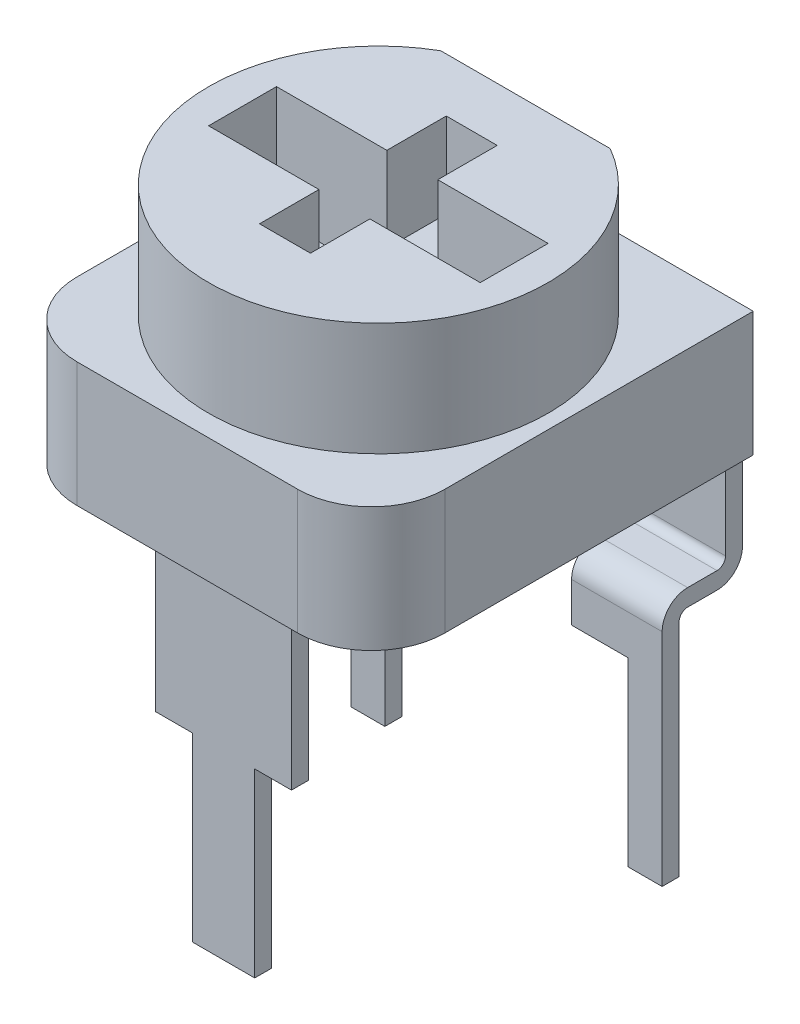
SolidWorks part; units mm, degrees
ref_plane "Plan de face" through (0, 0, 0) normal (0, 0, 1) x (1, 0, 0)
ref_plane "Plan de dessus" through (0, 0, 0) normal (0, 1, 0) x (1, 0, 0)
ref_plane "Plan de droite" through (0, 0, 0) normal (1, 0, 0) x (0, 0, -1)
sketch "Esquisse1" plane through (0, 0, 0) normal (0, 1, 0) x (1, 0, 0)
  line L0 (-1.4967, 2.6) -> (1.4967, 2.6)
  line L2 (-2.4, -0.6) -> (2.4, -0.6)
  line L3 (-2.4, -0.6) -> (-2.4, 0.6)
  line L4 (-2.4, 0.6) -> (2.4, 0.6)
  line L5 (2.4, -0.6) -> (2.4, 0.6)
  line L6 (-2.4, -0.6) -> (2.4, 0.6) construction
  line L7 (-2.4, 0.6) -> (2.4, -0.6) construction
  arc A0 (-1.4967, 2.6) -> (1.4967, 2.6) centre (0, 0) ccw
  dimension "D1" = 3
  dimension "D2" = 2.6
  dimension "D3" = 4.8
  dimension "D4" = 1.2
extrude "Boss.-Extru.1" add sketch "Esquisse1" along normal blind 2
sketch "Esquisse2" plane through (0, 2, 0) normal (0, 1, 0) x (-1, 0, 0)
  line L1 (0.45, 1.65) -> (-0.45, 1.65)
  line L2 (0.45, 1.65) -> (0.45, -1.65)
  line L3 (0.45, -1.65) -> (-0.45, -1.65)
  line L4 (-0.45, 1.65) -> (-0.45, -1.65)
  line L5 (0.45, 1.65) -> (-0.45, -1.65) construction
  line L6 (0.45, -1.65) -> (-0.45, 1.65) construction
  point P0 (0, 0)
  dimension "D1" = 0.9
  dimension "D2" = 3.3
extrude "Enlèv. mat.-Extru.1" cut sketch "Esquisse2" against normal blind 1.5
sketch "Esquisse3" plane through (0, 0, 0) normal (0, 1, 0) x (1, 0, 0)
  line L1 (-1.95, -3.375) -> (1.95, -3.375)
  line L2 (-3.25, -2.075) -> (-3.25, 3.375)
  line L3 (-3.25, 3.375) -> (3.25, 3.375)
  line L4 (3.25, -2.075) -> (3.25, 3.375)
  line L5 (-3.25, -3.375) -> (3.25, 3.375) construction
  line L6 (-3.25, 3.375) -> (3.25, -3.375) construction
  arc A0 (1.95, -3.375) -> (3.25, -2.075) centre (1.95, -2.075) ccw
  arc A1 (-1.95, -3.375) -> (-3.25, -2.075) centre (-1.95, -2.075) cw
  point P0 (0, 0)
  dimension "D3" = 1.3
  dimension "D1" = 6.5
  dimension "D2" = 6.75
  dimension "D4" = 3.375
extrude "Boss.-Extru.2" add sketch "Esquisse3" against normal blind 2.2
sketch "Esquisse4" plane through (0, 0, 0) normal (1, 0, 0) x (0, 0, -1)
  line L0 (0.5438, -1) -> (3.235, -1)
  line L1 (3.535, -1.3) -> (3.535, -4)
  line L2 (3.235, -4.3) -> (2.715, -4.3)
  line L3 (2.415, -4.6) -> (2.415, -8.5)
  line L4 (3.375, -2.2) -> (3.375, 0) construction
  line L5 (-2.075, 0) -> (3.375, 0) construction
  arc A0 (2.715, -4.3) -> (2.415, -4.6) centre (2.715, -4.6) ccw
  arc A1 (3.535, -4) -> (3.235, -4.3) centre (3.235, -4) cw
  arc A2 (3.235, -1) -> (3.535, -1.3) centre (3.235, -1.3) cw
  dimension "D1" = 0.3
  dimension "D2" = 1.12
  dimension "D3" = 7.5
  dimension "D4" = 4.2
  dimension "D5" = 0.16
  dimension "D6" = 1
extrude "Extru.-Mince1" add sketch "Esquisse4" along normal mid plane 1.6 from offset 1.95 thin offset against normal yes
pattern_linear "Répétition linéaire1" count 2 spacing 3.9 along (1, 0, 0) of "Extru.-Mince1"
sketch "Esquisse5" plane through (0, 0, 0) normal (1, 0, 0) x (0, 0, -1)
  line L0 (-2.585, -8.5) -> (-2.585, -2.2)
  line L1 (-2.075, -2.2) -> (3.375, -2.2) construction
  line L2 (2.565, -8.5) -> (2.265, -8.5) construction
  point P5 (2.415, -8.5)
  dimension "D1" = 5
extrude "Extru.-Mince2" add sketch "Esquisse5" along normal mid plane 2.4 thin thin type mid plane wall 0.3
sketch "Esquisse6" plane through (0, 0, -2.565) normal (0, 0, -1) x (-1, 0, 0)
  line L0 (-2.75, -8.5) -> (-1.15, -8.5) construction
  line L1 (-2.15, -8.5) -> (-0.55, -8.5)
  line L2 (-2.15, -8.5) -> (-2.15, -5.3)
  line L3 (-2.15, -5.3) -> (-0.55, -5.3)
  line L4 (-0.55, -8.5) -> (-0.55, -5.3)
  line L5 (-2.75, -4.6) -> (-2.75, -8.5) construction
  line L6 (1.15, -8.5) -> (2.75, -8.5) construction
  line L7 (0.55, -5.3) -> (2.15, -5.3)
  line L8 (0.55, -5.3) -> (0.55, -8.5)
  line L9 (0.55, -8.5) -> (2.15, -8.5)
  line L10 (2.15, -5.3) -> (2.15, -8.5)
  line L11 (2.75, -4.6) -> (2.75, -8.5) construction
  dimension "D1" = 1.6
  dimension "D2" = 3.2
  dimension "D3" = 0.6
  dimension "D5" = 0.6
extrude "Enlèv. mat.-Extru.2" cut sketch "Esquisse6" against normal through all
